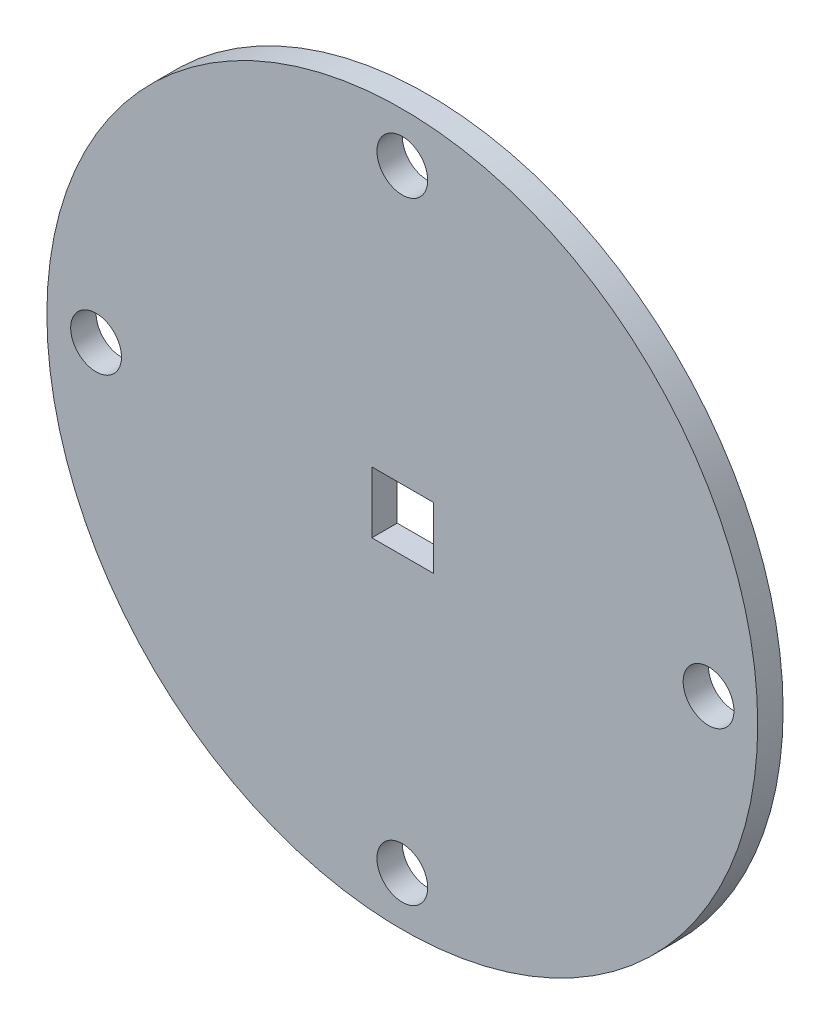
SolidWorks part; units mm, degrees
ref_plane "Front Plane" through (0, 0, 0) normal (0, 0, 1) x (1, 0, 0)
ref_plane "Top Plane" through (0, 0, 0) normal (0, 1, 0) x (1, 0, 0)
ref_plane "Right Plane" through (0, 0, 0) normal (1, 0, 0) x (0, 0, -1)
sketch "Sketch1" plane through (0, 0, 0) normal (0, 0, 1) x (1, 0, 0)
  line L1 (-6, -6.15) -> (6.1, -6.15)
  line L2 (-6, -6.15) -> (-6, 5.95)
  line L3 (-6, 5.95) -> (6.1, 5.95)
  line L4 (6.1, -6.15) -> (6.1, 5.95)
  circle A0 centre (0, 0) radius 70
  circle A3 centre (0, 60.31) radius 5
  circle A4 centre (60.31, 0) radius 5
  circle A5 centre (0, -60.31) radius 5
  circle A6 centre (-60.31, 0) radius 5
  point P20 (0, 0)
  dimension "D1" = 4
extrude "Boss-Extrude1" add sketch "Sketch1" along normal blind 5
